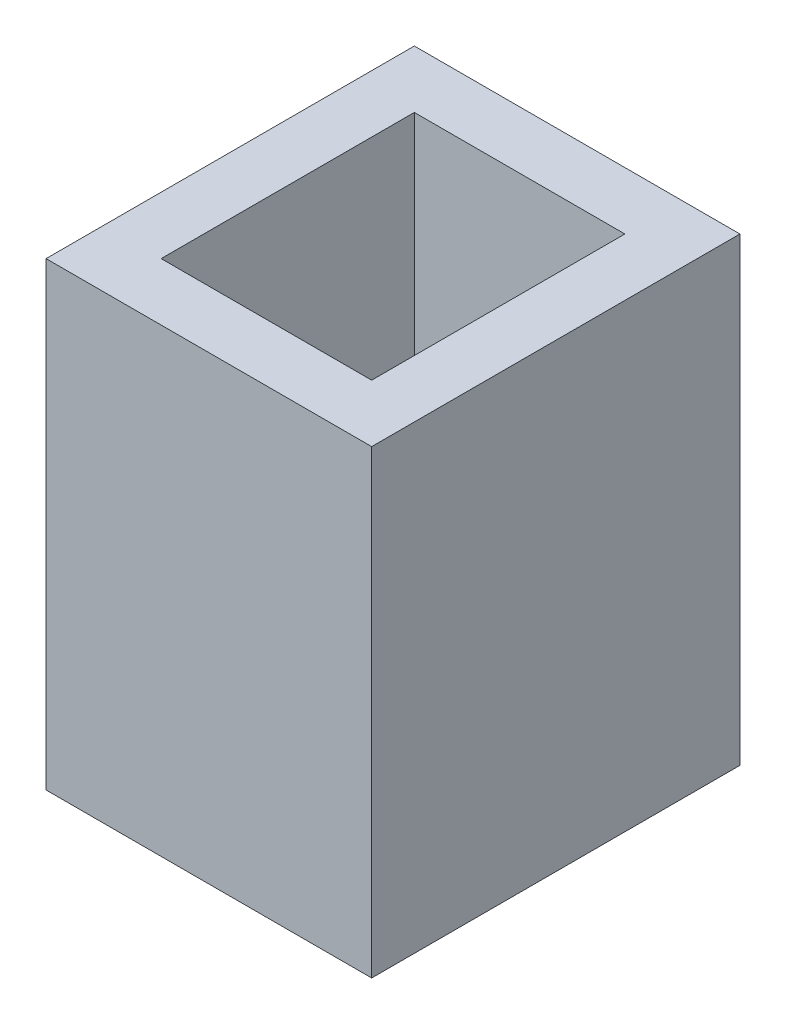
SolidWorks part; units mm, degrees
ref_plane "Front Plane" through (0, 0, 0) normal (0, 0, 1) x (1, 0, 0)
ref_plane "Top Plane" through (0, 0, 0) normal (0, 1, 0) x (1, 0, 0)
ref_plane "Right Plane" through (0, 0, 0) normal (1, 0, 0) x (0, 0, -1)
sketch "Sketch1" plane through (0, 0, 0) normal (0, 1, 0) x (1, 0, 0)
  line L1 (-8.9852, -10.1625) -> (8.9853, -10.1625)
  line L2 (-8.9852, -10.1625) -> (-8.9853, 10.1625)
  line L3 (-8.9853, 10.1625) -> (8.9853, 10.1625)
  line L4 (8.9853, -10.1625) -> (8.9853, 10.1625)
  line L5 (0, 10.1625) -> (0, -10.1625) construction
  line L6 (-8.9852, 0) -> (8.9853, 0) construction
  line L7 (-5.8102, -6.9875) -> (5.8103, -6.9875)
  line L8 (-5.8102, -6.9875) -> (-5.8103, 6.9875)
  line L9 (-5.8103, 6.9875) -> (5.8102, 6.9875)
  line L10 (5.8103, -6.9875) -> (5.8102, 6.9875)
  line L11 (0, 6.9875) -> (0, -6.9875) construction
  line L12 (-5.8102, 0) -> (5.8103, 0) construction
  point P0 (0, 0)
  point P4 (0, 0)
  dimension "D1" = 13.9751
  dimension "D2" = 11.6205
  dimension "D3" = 3.175
  dimension "D4" = 3.175
extrude "Boss-Extrude1" add sketch "Sketch1" along normal blind 25.4
